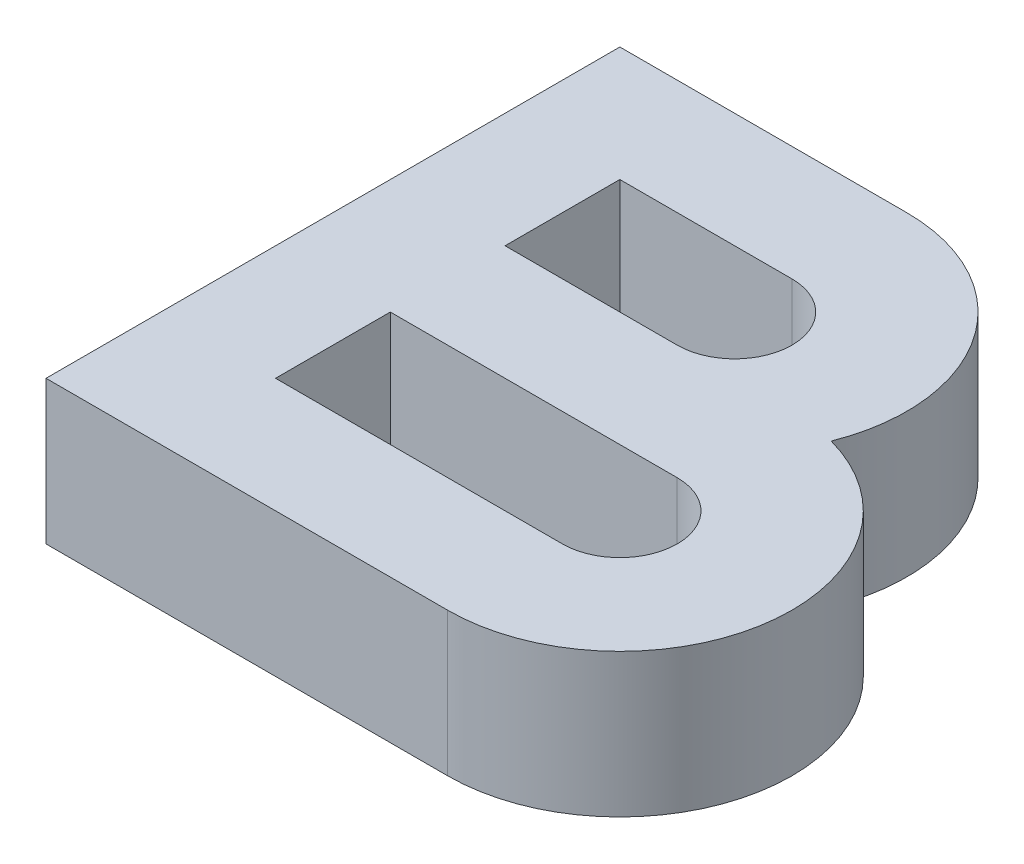
SolidWorks part; units mm, degrees
ref_plane "Front Plane" through (0, 0, 0) normal (0, 0, 1) x (1, 0, 0)
ref_plane "Top Plane" through (0, 0, 0) normal (0, 1, 0) x (1, 0, 0)
ref_plane "Right Plane" through (0, 0, 0) normal (1, 0, 0) x (0, 0, -1)
sketch "Sketch1" plane through (0, 0, 0) normal (0, 1, 0) x (1, 0, 0)
  line L0 (50, 0) -> (50, 40)
  line L1 (50, 40) -> (70, 40)
  line L2 (50, 0) -> (78, 0)
  line L3 (58, 32) -> (58, 24)
  line L4 (58, 24) -> (70, 24)
  line L5 (58, 32) -> (70, 32)
  line L6 (58, 8) -> (78, 8)
  line L7 (78, 16) -> (58, 16)
  line L8 (58, 16) -> (58, 8)
  arc A0 (70, 40) -> (81.1554, 23.5777) centre (70, 28) cw
  arc A1 (78, 0) -> (81.1554, 23.5777) centre (78, 12) ccw
  arc A2 (70, 24) -> (70, 32) centre (70, 28) ccw
  arc A3 (78, 8) -> (78, 16) centre (78, 12) ccw
  point P2 (0, 0)
  point P3 (0, 0)
  point P18 (0, 0)
  dimension "D8" = 4
  dimension "D1" = 40
  dimension "D2" = 50
  dimension "D3" = 40
  dimension "D4" = 32
  dimension "D5" = 8
  dimension "D6" = 8
  dimension "D7" = 8
  dimension "D9" = 8
extrude "Boss-Extrude1" add sketch "Sketch1" along normal blind 10
